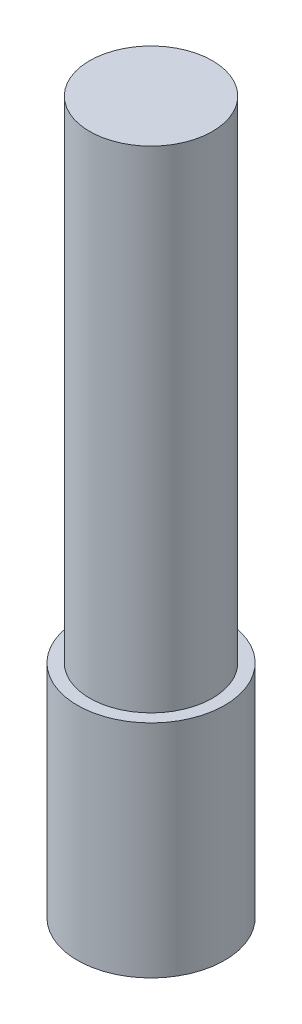
SolidWorks part; units mm, degrees
material "AISI 1020"
ref_plane "Front Plane" through (0, 0, 0) normal (0, 0, 1) x (1, 0, 0)
ref_plane "Top Plane" through (0, 0, 0) normal (0, 1, 0) x (1, 0, 0)
ref_plane "Right Plane" through (0, 0, 0) normal (1, 0, 0) x (0, 0, -1)
sketch "Sketch1" plane through (0, 0, 0) normal (0, 0, 1) x (1, 0, 0)
  line L0 (0, 0) -> (0, 29) construction
  line L1 (3, 0) -> (3, 9)
  line L2 (3, 9) -> (2.5, 9)
  line L3 (2.5, 9) -> (2.5, 29)
  line L4 (2.5, 29) -> (0, 29)
  line L5 (3, 0) -> (0, 0)
  line L6 (0, 0) -> (0, 29)
  dimension "D1" = 29
  dimension "D2" = 3
  dimension "D3" = 2.5
  dimension "D4" = 9
  dimension "D5" = 0
revolve "Revolve1" add sketch "Sketch1" angle 360 about L0
